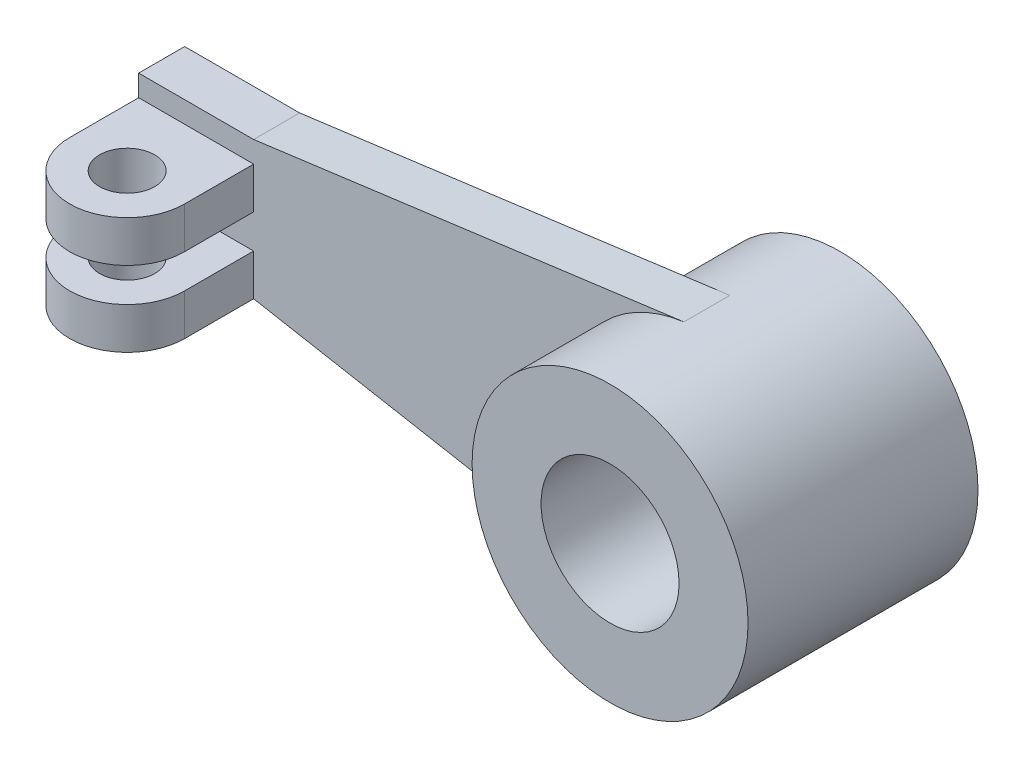
SolidWorks part; units mm, degrees
ref_plane "Front Plane" through (0, 0, 0) normal (0, 0, 1) x (1, 0, 0)
ref_plane "Top Plane" through (0, 0, 0) normal (0, 1, 0) x (1, 0, 0)
ref_plane "Right Plane" through (0, 0, 0) normal (1, 0, 0) x (0, 0, -1)
sketch "Sketch1" plane through (0, 0, 0) normal (0, 0, 1) x (1, 0, 0)
  circle A0 centre (0, 0) radius 15
  circle A1 centre (0, 0) radius 30
  dimension "D1" = 30
  dimension "D2" = 60
extrude "Boss-Extrude1" add sketch "Sketch1" along normal mid plane 50
sketch "Sketch2" plane through (0, 0, 0) normal (0, 0, 1) x (1, 0, 0)
  line L0 (-3.9486, 29.739) -> (-97.5, 17.3176)
  line L1 (-97.5, 17.3176) -> (-122.5, 17.3176)
  line L2 (-122.5, 17.3176) -> (-122.5, -12.6824)
  line L3 (-122.5, -12.6824) -> (-97.5, -12.6824)
  line L4 (-97.5, -12.6824) -> (-5.392, -29.5115)
  circle A0 centre (0, 0) radius 30 construction
  arc A1 (-3.9486, 29.739) -> (-5.392, -29.5115) centre (0, 0) ccw
  dimension "D1" = 25
  dimension "D2" = 30
  dimension "D3" = 122.5
  dimension "D4" = 3.9486
extrude "Boss-Extrude2" add sketch "Sketch2" along normal mid plane 10
sketch "Sketch3" plane through (0, -12.6824, 0) normal (0, -1, 0) x (1, 0, 0)
  line L0 (-122.5, 5) -> (-97.5, 5)
  line L1 (-97.5, 5) -> (-97.5, 20)
  line L2 (-97.5, 5) -> (-97.5, -5) construction
  line L3 (-122.5, 20) -> (-122.5, 5)
  line L4 (-122.5, -5) -> (-97.5, -5) construction
  arc A0 (-122.5, 20) -> (-97.5, 20) centre (-110, 20) cw
  circle A1 centre (-110, 20) radius 6
  dimension "D1" = 12.5
  dimension "D2" = 12
  dimension "D3" = 15
  dimension "D4" = 10
extrude "Boss-Extrude4" add sketch "Sketch3" against normal blind 9
mirror "Mirror1" about plane through (0, 0, 0) normal (0, 1, 0) of "Boss-Extrude4"
